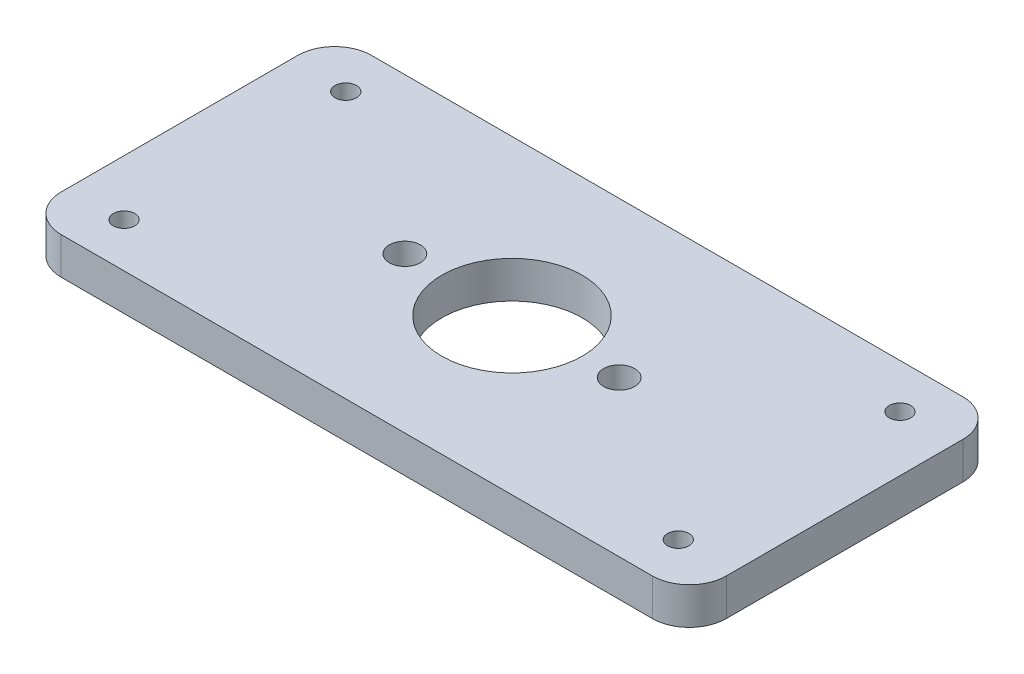
SolidWorks part; units mm, degrees
material "Acrylic (Medium-high impact)"
ref_plane "Front Plane" through (0, 0, 0) normal (0, 0, 1) x (1, 0, 0)
ref_plane "Top Plane" through (0, 0, 0) normal (0, 1, 0) x (1, 0, 0)
ref_plane "Right Plane" through (0, 0, 0) normal (1, 0, 0) x (0, 0, -1)
sketch "Sketch1" plane through (0, 0, 0) normal (0, 1, 0) x (1, 0, 0)
  line L0 (0, 21) -> (90, 21) construction
  line L1 (0, 0) -> (90, 0)
  line L2 (0, 0) -> (0, 42)
  line L3 (0, 42) -> (90, 42)
  line L4 (90, 0) -> (90, 42)
  line L5 (45, 42) -> (45, 0) construction
  line L6 (7.5, 42) -> (7.5, 0) construction
  circle A0 centre (45, 21) radius 9.5
  circle A1 centre (59.5, 21) radius 2.1
  circle A2 centre (30.5, 21) radius 2.1
  circle A3 centre (7.5, 36) radius 1.45
  circle A4 centre (7.5, 6) radius 1.45
  circle A5 centre (82.5, 6) radius 1.45
  circle A6 centre (82.5, 36) radius 1.45
  dimension "D3" = 19
  dimension "D4" = 4.2
  dimension "D5" = 29
  dimension "D6" = 2.9
  dimension "D7" = 30
  dimension "D1" = 90
  dimension "D2" = 42
  dimension "D8" = 7.5
extrude "Boss-Extrude1" add sketch "Sketch1" along normal blind 5
fillet "Fillet1" radius 5 4 edges at (90, 2.5, -42) (90, 2.5, 0) (0, 2.5, 0) (0, 2.5, -42)
sketch "Sketch3" plane through (0, 5, 0) normal (0, 1, 0) x (1, 0, 0)
  circle A1 centre (82.5, 36) radius 1.45 construction
  circle A2 centre (82.5, 6) radius 1.45 construction
  circle A3 centre (7.5, 6) radius 1.45 construction
  circle A4 centre (7.5, 36) radius 1.45 construction
  arc A5 (83.8611, 35.5) -> (83.8611, 36.5) centre (82.5, 36) ccw
  arc A6 (81.1389, 6.5) -> (81.1389, 5.5) centre (82.5, 6) ccw
  arc A7 (8.8611, 5.5) -> (8.8611, 6.5) centre (7.5, 6) ccw
  arc A8 (8.8611, 35.5) -> (8.8611, 36.5) centre (7.5, 36) ccw
  arc A9 (8.8611, 34.5) -> (8.8611, 35.5) centre (7.5, 35) ccw
  arc A10 (8.8611, 4.5) -> (8.8611, 5.5) centre (7.5, 5) ccw
  arc A11 (81.1389, 5.5) -> (81.1389, 4.5) centre (82.5, 5) ccw
  arc A12 (83.8611, 34.5) -> (83.8611, 35.5) centre (82.5, 35) ccw
  arc A13 (8.8611, 33.5) -> (8.8611, 34.5) centre (7.5, 34) ccw
  arc A14 (8.8611, 3.5) -> (8.8611, 4.5) centre (7.5, 4) ccw
  arc A15 (81.1389, 4.5) -> (81.1389, 3.5) centre (82.5, 4) ccw
  arc A16 (83.8611, 33.5) -> (83.8611, 34.5) centre (82.5, 34) ccw
  arc A17 (8.8611, 32.5) -> (8.8611, 33.5) centre (7.5, 33) ccw
  arc A18 (8.8611, 2.5) -> (8.8611, 3.5) centre (7.5, 3) ccw
  arc A19 (81.1389, 3.5) -> (81.1389, 2.5) centre (82.5, 3) ccw
  arc A20 (83.8611, 32.5) -> (83.8611, 33.5) centre (82.5, 33) ccw
  arc A21 (6.1389, 32.5) -> (8.8611, 32.5) centre (7.5, 32) ccw
  arc A22 (6.1389, 2.5) -> (8.8611, 2.5) centre (7.5, 2) ccw
  arc A23 (81.1389, 2.5) -> (83.8611, 2.5) centre (82.5, 2) ccw
  arc A24 (81.1389, 32.5) -> (83.8611, 32.5) centre (82.5, 32) ccw
  arc A25 (8.8611, 36.5) -> (8.8611, 37.5) centre (7.5, 37) ccw
  arc A26 (83.8611, 36.5) -> (83.8611, 37.5) centre (82.5, 37) ccw
  arc A27 (81.1389, 7.5) -> (81.1389, 6.5) centre (82.5, 7) ccw
  arc A28 (8.8611, 6.5) -> (8.8611, 7.5) centre (7.5, 7) ccw
  arc A29 (8.8611, 37.5) -> (8.8611, 38.5) centre (7.5, 38) ccw
  arc A30 (83.8611, 37.5) -> (83.8611, 38.5) centre (82.5, 38) ccw
  arc A31 (81.1389, 8.5) -> (81.1389, 7.5) centre (82.5, 8) ccw
  arc A32 (8.8611, 7.5) -> (8.8611, 8.5) centre (7.5, 8) ccw
  arc A33 (8.8611, 38.5) -> (8.8611, 39.5) centre (7.5, 39) ccw
  arc A34 (83.8611, 38.5) -> (83.8611, 39.5) centre (82.5, 39) ccw
  arc A35 (81.1389, 9.5) -> (81.1389, 8.5) centre (82.5, 9) ccw
  arc A36 (8.8611, 8.5) -> (8.8611, 9.5) centre (7.5, 9) ccw
  arc A37 (8.8611, 39.5) -> (6.1389, 39.5) centre (7.5, 40) ccw
  arc A38 (83.8611, 39.5) -> (81.1389, 39.5) centre (82.5, 40) ccw
  arc A39 (83.8611, 9.5) -> (81.1389, 9.5) centre (82.5, 10) ccw
  arc A40 (8.8611, 9.5) -> (6.1389, 9.5) centre (7.5, 10) ccw
  arc A41 (6.1389, 33.5) -> (6.1389, 32.5) centre (7.5, 33) ccw
  arc A42 (6.1389, 34.5) -> (6.1389, 33.5) centre (7.5, 34) ccw
  arc A43 (6.1389, 35.5) -> (6.1389, 34.5) centre (7.5, 35) ccw
  arc A44 (6.1389, 36.5) -> (6.1389, 35.5) centre (7.5, 36) ccw
  arc A45 (6.1389, 37.5) -> (6.1389, 36.5) centre (7.5, 37) ccw
  arc A46 (6.1389, 38.5) -> (6.1389, 37.5) centre (7.5, 38) ccw
  arc A47 (6.1389, 39.5) -> (6.1389, 38.5) centre (7.5, 39) ccw
  arc A48 (6.1389, 3.5) -> (6.1389, 2.5) centre (7.5, 3) ccw
  arc A49 (6.1389, 4.5) -> (6.1389, 3.5) centre (7.5, 4) ccw
  arc A50 (6.1389, 5.5) -> (6.1389, 4.5) centre (7.5, 5) ccw
  arc A51 (6.1389, 6.5) -> (6.1389, 5.5) centre (7.5, 6) ccw
  arc A52 (6.1389, 7.5) -> (6.1389, 6.5) centre (7.5, 7) ccw
  arc A53 (6.1389, 8.5) -> (6.1389, 7.5) centre (7.5, 8) ccw
  arc A54 (6.1389, 9.5) -> (6.1389, 8.5) centre (7.5, 9) ccw
  arc A55 (83.8611, 8.5) -> (83.8611, 9.5) centre (82.5, 9) ccw
  arc A56 (83.8611, 7.5) -> (83.8611, 8.5) centre (82.5, 8) ccw
  arc A57 (83.8611, 6.5) -> (83.8611, 7.5) centre (82.5, 7) ccw
  arc A58 (83.8611, 5.5) -> (83.8611, 6.5) centre (82.5, 6) ccw
  arc A59 (83.8611, 4.5) -> (83.8611, 5.5) centre (82.5, 5) ccw
  arc A60 (83.8611, 3.5) -> (83.8611, 4.5) centre (82.5, 4) ccw
  arc A61 (83.8611, 2.5) -> (83.8611, 3.5) centre (82.5, 3) ccw
  arc A62 (81.1389, 33.5) -> (81.1389, 32.5) centre (82.5, 33) ccw
  arc A63 (81.1389, 34.5) -> (81.1389, 33.5) centre (82.5, 34) ccw
  arc A64 (81.1389, 35.5) -> (81.1389, 34.5) centre (82.5, 35) ccw
  arc A65 (81.1389, 36.5) -> (81.1389, 35.5) centre (82.5, 36) ccw
  arc A66 (81.1389, 37.5) -> (81.1389, 36.5) centre (82.5, 37) ccw
  arc A67 (81.1389, 38.5) -> (81.1389, 37.5) centre (82.5, 38) ccw
  arc A68 (81.1389, 39.5) -> (81.1389, 38.5) centre (82.5, 39) ccw
  dimension "D4" = 1
  dimension "D2" = 1
  dimension "D1" = 5
  dimension "D3" = 5
extrude "Cut-Extrude1" [suppressed] cut sketch "Sketch3" against normal through all
